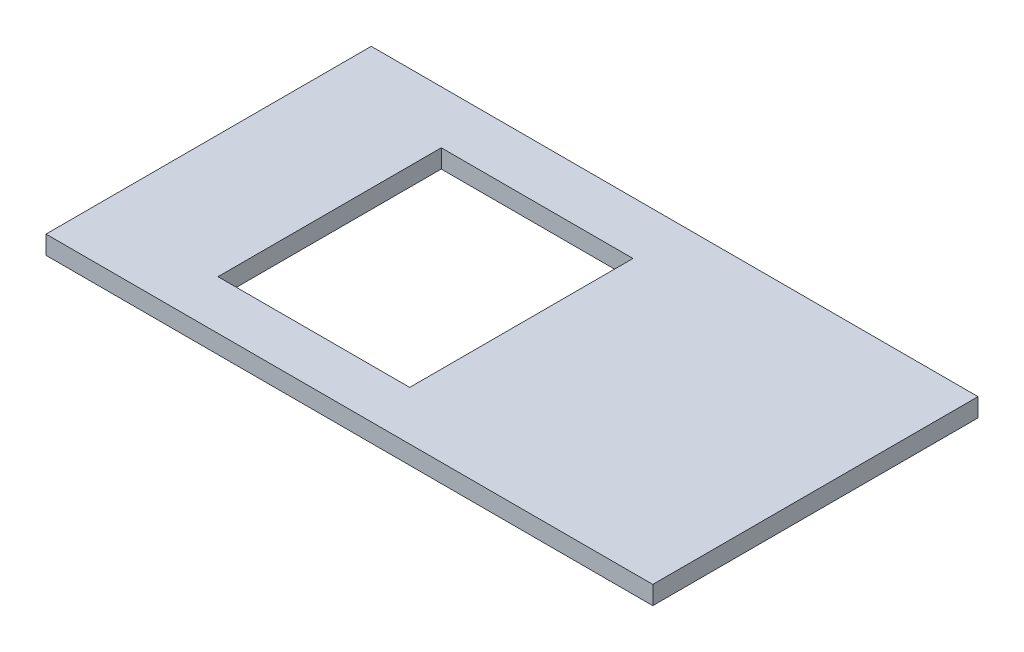
SolidWorks part; units mm, degrees
ref_plane "Спереди" through (0, 0, 0) normal (0, 0, 1) x (1, 0, 0)
ref_plane "Сверху" through (0, 0, 0) normal (0, 1, 0) x (1, 0, 0)
ref_plane "Справа" through (0, 0, 0) normal (1, 0, 0) x (0, 0, -1)
sketch "Эскиз1" plane through (0, 0, 0) normal (0, 1, 0) x (1, 0, 0)
  line L0 (0, 0) -> (0, 670)
  line L1 (0, 670) -> (1250, 670)
  line L2 (1250, 670) -> (1250, 0)
  line L5 (1250, 0) -> (0, 0)
  dimension "D1" = 670
  dimension "D2" = 1250
extrude "Бобышка-Вытянуть1" add sketch "Эскиз1" along normal blind 38
sketch "Эскиз2" plane through (0, 38, 0) normal (0, 1, 0) x (1, 0, 0)
  line L1 (253.1553, 561.1164) -> (648.1553, 561.1164)
  line L2 (253.1553, 561.1164) -> (253.1553, 101.1164)
  line L3 (253.1553, 101.1164) -> (648.1553, 101.1164)
  line L4 (648.1553, 561.1164) -> (648.1553, 101.1164)
extrude "Вырез-Вытянуть1" cut sketch "Эскиз2" against normal through all
